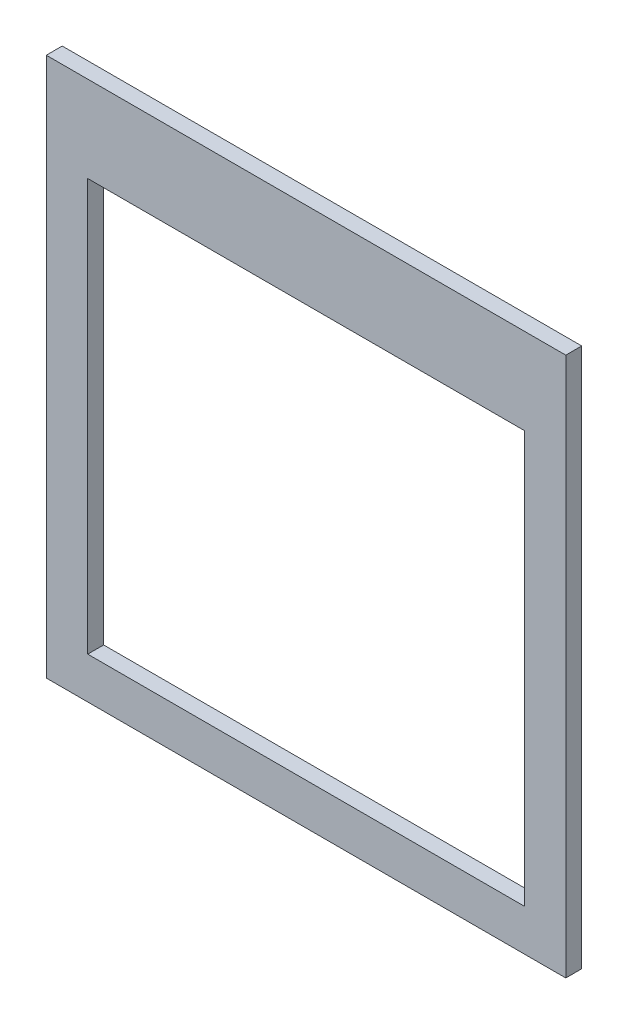
SolidWorks part; units mm, degrees
ref_plane "Спереди" through (0, 0, 0) normal (0, 0, 1) x (1, 0, 0)
ref_plane "Сверху" through (0, 0, 0) normal (0, 1, 0) x (1, 0, 0)
ref_plane "Справа" through (0, 0, 0) normal (1, 0, 0) x (0, 0, -1)
sketch "Эскиз1" plane through (0, 0, 0) normal (0, 0, 1) x (1, 0, 0)
  line L1 (303.2282, -332.1313) -> (-22.7718, -332.1313)
  line L2 (303.2282, -332.1313) -> (303.2282, 6.3687)
  line L3 (303.2282, 6.3687) -> (-22.7718, 6.3687)
  line L4 (-22.7718, -332.1313) -> (-22.7718, 6.3687)
  line L5 (3.2282, -47.6313) -> (277.2282, -47.6313)
  line L6 (3.2282, -47.6313) -> (3.2282, -306.1313)
  line L7 (3.2282, -306.1313) -> (277.2282, -306.1313)
  line L8 (277.2282, -47.6313) -> (277.2282, -306.1313)
  dimension "D1" = 338.5
  dimension "D2" = 326
  dimension "D3" = 26
  dimension "D4" = 26
  dimension "D5" = 26
  dimension "D6" = 54
extrude "Бобышка-Вытянуть1" add sketch "Эскиз1" along normal blind 10
